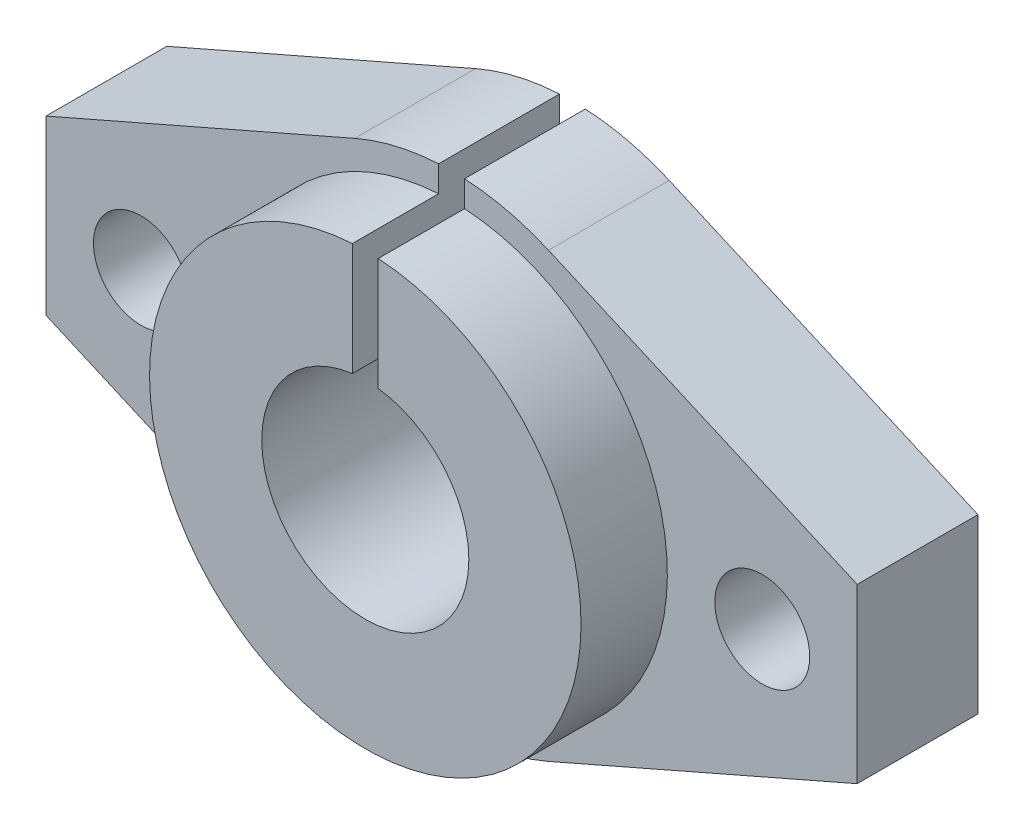
SolidWorks part; units mm, degrees
ref_plane "Front Plane" through (0, 0, 0) normal (0, 0, 1) x (1, 0, 0)
ref_plane "Top Plane" through (0, 0, 0) normal (0, 1, 0) x (1, 0, 0)
ref_plane "Right Plane" through (0, 0, 0) normal (1, 0, 0) x (0, 0, -1)
sketch "Sketch1" plane through (0, 0, 0) normal (0, 0, 1) x (1, 0, 0)
  line L0 (-5.6114, 12.8262) -> (-23.5, 5)
  line L1 (23.5, -5) -> (-23.5, -5) construction
  line L2 (23.5, -5) -> (23.5, 5)
  line L3 (23.5, 5) -> (-23.5, 5) construction
  line L4 (-23.5, -5) -> (-23.5, 5)
  line L5 (23.5, -5) -> (-23.5, 5) construction
  line L6 (23.5, 5) -> (-23.5, -5) construction
  line L7 (5.6114, 12.8262) -> (23.5, 5)
  line L8 (-5.6114, -12.8262) -> (-23.5, -5)
  line L9 (5.6114, -12.8262) -> (23.5, -5)
  arc A0 (-5.6114, -12.8262) -> (5.6114, -12.8262) centre (0, 0) ccw
  arc A2 (5.6114, 12.8262) -> (-5.6114, 12.8262) centre (0, 0) ccw
  dimension "D1" = 28
  dimension "D2" = 47
  dimension "D3" = 10
extrude "Boss-Extrude1" add sketch "Sketch1" along normal blind 7
sketch "Sketch2" plane through (0, 0, 7) normal (0, 0, 1) x (1, 0, 0)
  circle A0 centre (0, 0) radius 12.5
  dimension "D1" = 25
extrude "Boss-Extrude2" add sketch "Sketch2" along normal blind 5
sketch "Sketch3" plane through (0, 0, 12) normal (0, 0, 1) x (1, 0, 0)
  circle A0 centre (0, 0) radius 6
  dimension "D1" = 12
extrude "Cut-Extrude1" cut sketch "Sketch3" against normal through all
sketch "Sketch4" plane through (0, 0, 7) normal (0, 0, 1) x (1, 0, 0)
  line L0 (0, 0) -> (4.1906, 0) construction
  circle A0 centre (-18, 0) radius 2.75
  circle A1 centre (18, 0) radius 2.75
  dimension "D1" = 5.5
  dimension "D2" = 5.5
  dimension "D3" = 18
  dimension "D4" = 18
extrude "Cut-Extrude2" cut sketch "Sketch4" against normal through all
sketch "Sketch5" plane through (0, 0, 12) normal (0, 0, 1) x (1, 0, 0)
  line L0 (0, 0) -> (0, 17.7149) construction
  line L1 (-0.75, 25) -> (-0.75, 5)
  line L2 (-0.75, 25) -> (0.75, 25)
  line L3 (-0.75, 5) -> (0.75, 5)
  line L4 (0.75, 25) -> (0.75, 5)
  line L5 (-0.75, 25) -> (0.75, 5) construction
  line L6 (-0.75, 5) -> (0.75, 25) construction
  point P4 (0, 15)
  dimension "D1" = 1.5
  dimension "D2" = 20
  dimension "D3" = 15
extrude "Cut-Extrude3" cut sketch "Sketch5" against normal through all
